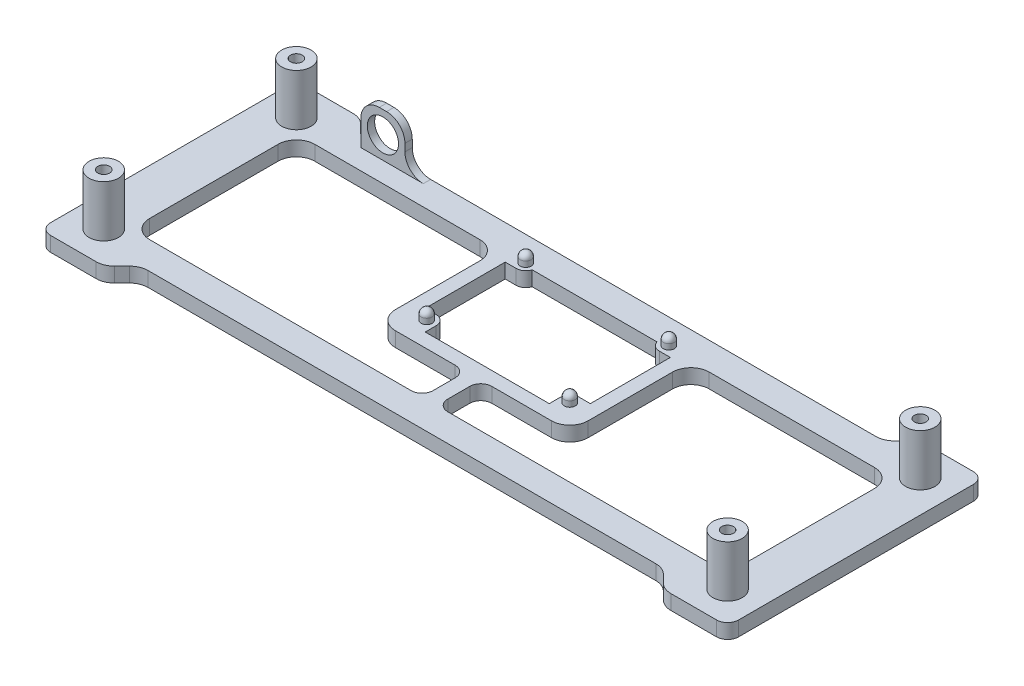
SolidWorks part; units mm, degrees
ref_plane "Front Plane" through (0, 0, 0) normal (0, 0, 1) x (1, 0, 0)
ref_plane "Top Plane" through (0, 0, 0) normal (0, 1, 0) x (1, 0, 0)
ref_plane "Right Plane" through (0, 0, 0) normal (1, 0, 0) x (0, 0, -1)
sketch "Sketch2" plane through (0, 0, 0) normal (0, 1, 0) x (1, 0, 0)
  line L0 (-85, 26.25) -> (85, 26.25) construction
  line L1 (-88.75, 30) -> (88.75, 30) construction
  line L2 (-88.75, 30) -> (-88.75, -30) construction
  line L3 (-88.75, -30) -> (88.75, -30) construction
  line L4 (88.75, 30) -> (88.75, -30) construction
  line L5 (85, 26.25) -> (85, -26.25) construction
  line L6 (-85, -26.25) -> (85, -26.25) construction
  line L7 (-85, 26.25) -> (-85, -26.25) construction
  line L8 (-93.75, -35) -> (-76.25, -35)
  line L9 (93.75, 35) -> (93.75, -35)
  line L10 (-93.75, 35) -> (-76.25, 35)
  line L11 (-93.75, 35) -> (-93.75, -35)
  line L14 (-71.25, -30) -> (71.25, -30)
  line L15 (-71.25, 30) -> (71.25, 30)
  line L16 (-76.25, 35) -> (-71.25, 30)
  line L17 (-71.25, -30) -> (-76.25, -35)
  line L18 (0, 40.6099) -> (0, -49.2062) construction
  line L19 (71.25, -30) -> (76.25, -35)
  line L20 (76.25, 35) -> (71.25, 30)
  line L21 (76.25, 35) -> (93.75, 35)
  line L22 (76.25, -35) -> (93.75, -35)
  line L23 (-93.75, 35) -> (93.75, 35) construction
  line L24 (-81.25, 22.5) -> (-81.25, -22.5)
  line L25 (-93.75, -35) -> (93.75, -35) construction
  line L26 (-81.25, -22.5) -> (81.25, -22.5)
  line L27 (81.25, 22.5) -> (81.25, -22.5)
  line L28 (-81.25, 22.5) -> (81.25, 22.5)
  circle A0 centre (-85, 26.25) radius 1.6
  circle A1 centre (85, 26.25) radius 1.6
  circle A2 centre (85, -26.25) radius 1.6
  circle A3 centre (-85, -26.25) radius 1.6
  point P4 (0, 30)
  point P6 (-88.75, 0)
  point P24 (0, 0)
  point P26 (0, 0)
  point P31 (0, 0)
  point P32 (0, 0)
  point P33 (70.2824, 30)
  dimension "D4" = 3.2
  dimension "D1" = 177.5
  dimension "D2" = 60
  dimension "D6" = 45
  dimension "D7" = 3.75
  dimension "D3" = 3.75
  dimension "D5" = 5
extrude "Boss-Extrude2" add sketch "Sketch2" along normal blind 4
fillet "Fillet3" radius 3 4 edges at (93.75, 2, -35) (93.75, 2, 35) (-93.75, 2, -35) (-93.75, 2, 35)
fillet "Fillet4" radius 5 12 edges at (81.25, 2, -22.5) (-81.25, 2, -22.5) (-81.25, 2, 22.5) (81.25, 2, 22.5) (-76.25, 2, -35) (-71.25, 2, -30) (71.25, 2, -30) (76.25, 2, -35) (76.25, 2, 35) (71.25, 2, 30) (-71.25, 2, 30) (-76.25, 2, 35)
sketch "Sketch5" plane through (0, 0, 0) normal (0, 1, 0) x (1, 0, 0)
  line L0 (-19.5, 23.25) -> (-19.5, -3.75) construction
  line L1 (-16.9, 26.25) -> (16.9, 26.25)
  line L2 (-22.5, 20.65) -> (-22.5, -1.15)
  line L3 (-16.9, -6.75) -> (16.9, -6.75)
  line L4 (22.5, 20.65) -> (22.5, -1.15)
  line L5 (-19.5, -3.75) -> (19.5, -3.75) construction
  line L6 (19.5, 23.25) -> (19.5, -3.75) construction
  line L7 (-19.5, 23.25) -> (19.5, 23.25) construction
  line L8 (0, 40.6099) -> (0, -49.2062) construction
  line L9 (-85, 26.25) -> (85, 26.25) construction
  line L10 (-26.25, -10.5) -> (-2, -10.5)
  line L11 (26.25, 30) -> (26.25, -10.5)
  line L12 (-26.25, 30) -> (26.25, 30)
  line L13 (-26.25, 30) -> (-26.25, -10.5)
  line L14 (-16.9, -3.75) -> (-16.9, -6.75)
  line L15 (-19.5, -1.15) -> (-22.5, -1.15)
  line L16 (0, 30) -> (0, -10.5) construction
  line L17 (16.9, -3.75) -> (16.9, -6.75)
  line L18 (19.5, -1.15) -> (22.5, -1.15)
  line L19 (-19.5, 9.75) -> (19.5, 9.75) construction
  line L20 (19.5, 20.65) -> (22.5, 20.65)
  line L21 (16.9, 23.25) -> (16.9, 26.25)
  line L22 (-16.9, 23.25) -> (-16.9, 26.25)
  line L23 (-19.5, 20.65) -> (-22.5, 20.65)
  line L25 (-22.5, -6.75) -> (22.5, -6.75) construction
  line L26 (-22.5, 26.25) -> (-22.5, -6.75) construction
  line L27 (22.5, 26.25) -> (22.5, -6.75) construction
  line L28 (-22.5, 26.25) -> (22.5, 26.25) construction
  line L29 (-2, -10.5) -> (-2, -25.9394)
  line L30 (-2, -25.9394) -> (2, -25.9394)
  line L31 (2, -10.5) -> (2, -25.9394)
  line L32 (2, -10.5) -> (26.25, -10.5)
  line L34 (-26.25, -10.5) -> (26.25, -10.5) construction
  circle A0 centre (-19.5, 23.25) radius 1.6 construction
  circle A1 centre (19.5, 23.25) radius 1.6 construction
  circle A2 centre (19.5, -3.75) radius 1.6 construction
  circle A3 centre (-19.5, -3.75) radius 1.6 construction
  arc A4 (-16.9, -3.75) -> (-19.5, -1.15) centre (-19.5, -3.75) ccw
  arc A5 (16.9, -3.75) -> (19.5, -1.15) centre (19.5, -3.75) cw
  arc A6 (16.9, 23.25) -> (19.5, 20.65) centre (19.5, 23.25) ccw
  arc A7 (-16.9, 23.25) -> (-19.5, 20.65) centre (-19.5, 23.25) cw
  point P44 (0, -25.9394)
  dimension "D4" = 3.2
  dimension "D6" = 5.2
  dimension "D1" = 33
  dimension "D2" = 45
  dimension "D7" = 4
  dimension "D3" = 3
  dimension "D5" = 3.75
extrude "Boss-Extrude3" add sketch "Sketch5" along normal blind 4
fillet "Fillet5" radius 5 4 edges at (-26.25, 2, -22.5) (26.25, 2, -22.5) (-26.25, 2, 10.5) (26.25, 2, 10.5)
sketch "Sketch7" plane through (0, 4, 0) normal (0, 1, 0) x (1, 0, 0)
  line L0 (-71.25, 30) -> (71.25, 30) construction
  line L1 (-69.1789, 28) -> (-57.1789, 28)
  line L2 (-69.1789, 28) -> (-69.1789, 30)
  line L3 (-69.1789, 30) -> (-57.1789, 30)
  line L4 (-57.1789, 28) -> (-57.1789, 30)
  point P7 (0, 0)
  point P8 (0, 0)
  dimension "D1" = 12
  dimension "D2" = 2
extrude "Boss-Extrude4" add sketch "Sketch7" along normal blind 12
sketch "Sketch8" plane through (0, 0, -30) normal (0, 0, -1) x (-1, 0, 0)
  line L0 (57.1789, 10) -> (69.1789, 10) construction
  line L1 (57.1789, 16) -> (57.1789, 4) construction
  line L2 (69.1789, 16) -> (69.1789, 4) construction
  circle A0 centre (63.1789, 10) radius 4.25
  dimension "D1" = 8.5
extrude "Cut-Extrude3" cut sketch "Sketch8" against normal up to next
fillet "Fillet6" radius 5 3 edges at (-57.1789, 4, -29) (-57.1789, 16, -29) (-69.1789, 16, -29)
fillet "Fillet7" radius 3 4 edges at (2, 2, 22.5) (2, 2, 10.5) (-2, 2, 22.5) (-2, 2, 10.5)
sketch "Sketch9" plane through (0, 4, 0) normal (0, 1, 0) x (1, 0, 0)
  circle A0 centre (-19.5, -3.75) radius 1.5
  circle A1 centre (-19.5, 23.25) radius 1.5
  circle A2 centre (19.5, 23.25) radius 1.5
  circle A3 centre (19.5, -3.75) radius 1.5
  dimension "D1" = 3
extrude "Boss-Extrude5" add sketch "Sketch9" along normal blind 3
fillet "Fillet8" radius 1.5 4 edges at (19.5, 7, 5.25) (19.5, 7, -21.75) (-19.5, 7, -21.75) (-19.5, 7, 5.25)
sketch "Sketch10" plane through (0, 4, 0) normal (0, 1, 0) x (1, 0, 0)
  circle A0 centre (-85, 26.25) radius 4
  circle A1 centre (85, 26.25) radius 4
  circle A2 centre (85, -26.25) radius 4
  circle A3 centre (-85, -26.25) radius 4
  circle A4 centre (85, 26.25) radius 1.6
  circle A5 centre (85, -26.25) radius 1.6
  circle A6 centre (-85, -26.25) radius 1.6
  circle A7 centre (-85, 26.25) radius 1.6
  dimension "D1" = 8
extrude "Boss-Extrude6" add sketch "Sketch10" along normal blind 14
